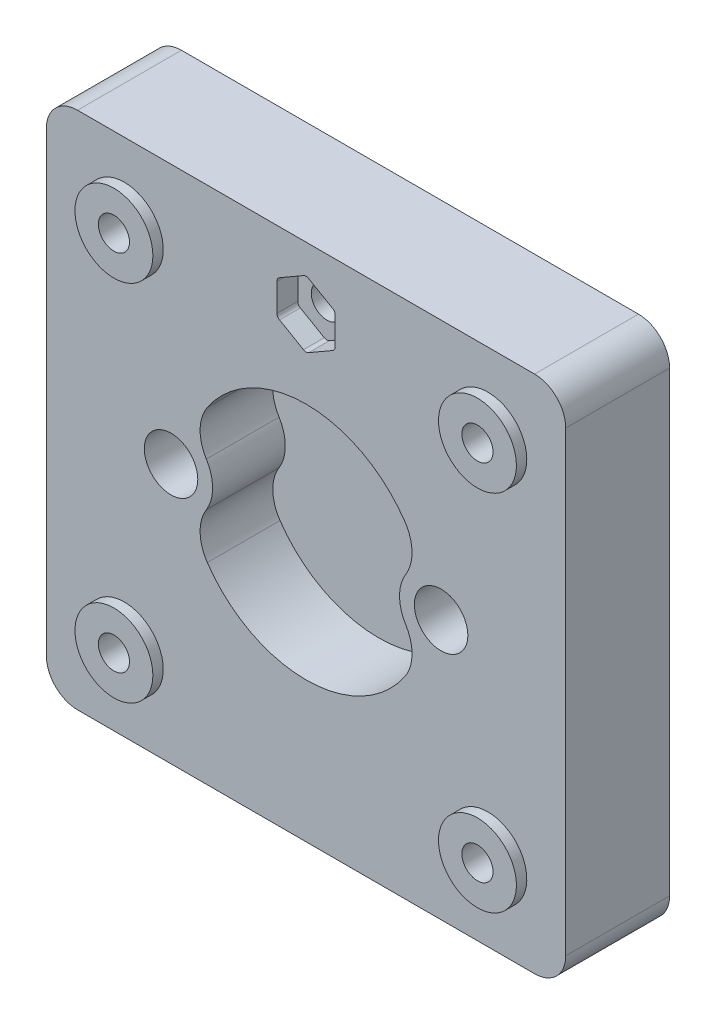
SolidWorks part; units mm, degrees
other "Anode"
ref_plane "Front Plane" through (0, 0, 0) normal (0, 0, 1) x (1, 0, 0)
ref_plane "Top Plane" through (0, 0, 0) normal (0, 1, 0) x (1, 0, 0)
ref_plane "Right Plane" through (0, 0, 0) normal (1, 0, 0) x (0, 0, -1)
sketch "Sketch1" plane through (0, 0, 0) normal (0, 1, 0) x (1, 0, 0)
  line L1 (25, -25) -> (-25, -25)
  line L2 (25, -25) -> (25, 25)
  line L3 (25, 25) -> (-25, 25)
  line L4 (-25, -25) -> (-25, 25)
  line L5 (25, -25) -> (-25, 25) construction
  line L6 (25, 25) -> (-25, -25) construction
  point P0 (0, 0)
  dimension "D1" = 50
  dimension "D2" = 50
extrude "Body" add sketch "Sketch1" along normal blind 10
sketch "Sketch2" plane through (0, 10, 0) normal (0, 1, 0) x (1, 0, 0)
  circle A0 centre (0, 0) radius 11.5
  dimension "D1" = 23
extrude "Cut view" cut sketch "Sketch2" against normal blind 7
fillet "FilletBody" radius 3 4 edges at (-25, 5, -25) (25, 5, -25) (25, 5, 25) (-25, 5, 25)
sketch "Sketch3" plane through (0, 10, 0) normal (0, 1, 0) x (1, 0, 0)
  line L0 (-25, 22) -> (-25, -22) construction
  line L1 (22, 25) -> (-22, 25) construction
  line L2 (-38.934, 0) -> (38.0552, 0) construction
  line L3 (0, 29.5616) -> (0, -31.3312) construction
  circle A0 centre (-17.5, 17.5) radius 3.75
  circle A1 centre (17.5, 17.5) radius 3.75
  circle A2 centre (17.5, -17.5) radius 3.75
  circle A3 centre (-17.5, -17.5) radius 3.75
  dimension "D1" = 7.5
  dimension "D2" = 7.5
  dimension "D3" = 7.5
extrude "Bolt extrude" add sketch "Sketch3" along normal blind 1
sketch "Sketch4" plane through (0, 11, 0) normal (0, 1, 0) x (1, 0, 0)
  line L2 (-40.7589, 0) -> (37.9331, 0) construction
  line L3 (-5.5, 0) -> (5.5, 0) construction
  line L4 (0, 29.2624) -> (0, -30.4072) construction
  circle A0 centre (-17.5, 17.5) radius 1.5
  circle A1 centre (17.5, 17.5) radius 1.5
  circle A2 centre (17.5, -17.5) radius 1.5
  circle A3 centre (-17.5, -17.5) radius 1.5
  dimension "D1" = 3
extrude "Bolt" cut sketch "Sketch4" against normal blind 16 and the other way blind 10
sketch "Sketch5" plane through (0, 10, 0) normal (0, 1, 0) x (1, 0, 0)
  line L0 (22, 25) -> (-22, 25) construction
  line L1 (0, 22.2332) -> (-2.8, 20.6166)
  line L2 (-2.8, 20.6166) -> (-2.8, 17.3834)
  line L3 (-2.8, 17.3834) -> (0, 15.7668)
  line L4 (0, 15.7668) -> (2.8, 17.3834)
  line L5 (2.8, 17.3834) -> (2.8, 20.6166)
  line L6 (2.8, 20.6166) -> (0, 22.2332)
  circle A0 centre (0, 19) radius 2.8 construction
  dimension "D2" = 5.6
  dimension "D1" = 6
extrude "Hex" cut sketch "Sketch5" against normal blind 2
sketch "Sketch19" plane through (0, 8, 0) normal (0, 1, 0) x (1, 0, 0)
  circle A0 centre (0, 19) radius 1.5
  dimension "D1" = 3
extrude "Hex_bolt" cut sketch "Sketch19" against normal blind 3
sketch "Sketch6" plane through (0, 10, 0) normal (0, 1, 0) x (1, 0, 0)
  line L0 (-5.5, 0) -> (5.5, 0) construction
  line L1 (-25, 22) -> (-25, -22) construction
  line L2 (0, 27.3129) -> (0, -30.0369) construction
  circle A0 centre (-13, 0) radius 4
  circle A1 centre (13, 0) radius 4
  dimension "D2" = 8
  dimension "D1" = 12
extrude "Field1" add sketch "Sketch6" against normal blind 7
fillet "Field2" radius 4 4 edges at (10.9712, 6.5, -3.4473) (10.9712, 6.5, 3.4473) (-10.9712, 6.5, 3.4473) (-10.9712, 6.5, -3.4473)
sketch "Sketch7" plane through (0, 10, 0) normal (0, 1, 0) x (1, 0, 0)
  line L0 (-5.5, 0) -> (5.5, 0) construction
  line L1 (-25, 22) -> (-25, -22) construction
  line L2 (0, 27.9755) -> (0, -30.6258) construction
  circle A0 centre (-13, 0) radius 2.575
  circle A1 centre (13, 0) radius 2.575
  dimension "D2" = 5.15
  dimension "D1" = 12
extrude "Ports1" add sketch "Sketch7" along normal blind 12
sketch "Sketch10" plane through (0, 22, 0) normal (0, 1, 0) x (1, 0, 0)
  line L0 (0, 29.9579) -> (0, -31.6237) construction
  circle A0 centre (-13, 0) radius 1.575
  circle A1 centre (13, 0) radius 1.575
  dimension "D1" = 3.15
extrude "Ports2" cut sketch "Sketch10" against normal blind 32 and the other way blind 12
sketch "Sketch11" plane through (0, 0, 0) normal (0, -1, 0) x (1, 0, 0)
  circle A0 centre (0, 0) radius 15
  circle A1 centre (0, 0) radius 20
  dimension "D1" = 30
  dimension "D2" = 40
extrude "Seal1" cut sketch "Sketch11" against normal blind 0.5 contours A1 A0
sketch "Sketch15" plane through (0, 0, 0) normal (0, -1, 0) x (1, 0, 0)
  line L0 (5.5, 0) -> (-5.5, 0) construction
  line L1 (-14, 0) -> (-12, 0)
  line L2 (-8, 0) -> (-6, 0)
  line L3 (3, 0) -> (5, 0)
  line L4 (9, 0) -> (11, 0)
  line L5 (-31.4935, 0) -> (32.7979, 0) construction
  arc A0 (-14, 0) -> (13.523, 3.6235) centre (0, 0) cw
  arc A1 (-8, 0) -> (7.2505, 3.3809) centre (0, 0) cw
  arc A2 (-12, 0) -> (11.5911, 3.1058) centre (0, 0) cw
  arc A3 (-6, 0) -> (5.4378, 2.5357) centre (0, 0) cw
  arc A4 (13.523, 3.6235) -> (11.5911, 3.1058) centre (12.557, 3.3646) cw
  arc A5 (7.2505, 3.3809) -> (5.4378, 2.5357) centre (6.3442, 2.9583) cw
  arc A6 (11, 0) -> (-10.3366, 3.7622) centre (0, 0) ccw
  arc A7 (9, 0) -> (-8.4572, 3.0782) centre (0, 0) ccw
  arc A8 (5, 0) -> (-3.5355, 3.5355) centre (0, 0) ccw
  arc A9 (3, 0) -> (-2.1213, 2.1213) centre (0, 0) ccw
  arc A10 (-10.3366, 3.7622) -> (-8.4572, 3.0782) centre (-9.3969, 3.4202) ccw
  arc A11 (-3.5355, 3.5355) -> (-2.1213, 2.1213) centre (-2.8284, 2.8284) ccw
  arc A12 (3, 0) -> (-2.1213, -2.1213) centre (0, 0) cw
  arc A13 (-3.5355, -3.5355) -> (-2.1213, -2.1213) centre (-2.8284, -2.8284) cw
  arc A14 (5, 0) -> (-3.5355, -3.5355) centre (0, 0) cw
  arc A15 (-8, 0) -> (7.2505, -3.3809) centre (0, 0) ccw
  arc A16 (-6, 0) -> (5.4378, -2.5357) centre (0, 0) ccw
  arc A17 (7.2505, -3.3809) -> (5.4378, -2.5357) centre (6.3442, -2.9583) ccw
  arc A18 (9, 0) -> (-8.4572, -3.0782) centre (0, 0) cw
  arc A19 (-10.3366, -3.7622) -> (-8.4572, -3.0782) centre (-9.3969, -3.4202) cw
  arc A20 (11, 0) -> (-10.3366, -3.7622) centre (0, 0) cw
  arc A21 (-14, 0) -> (13.523, -3.6235) centre (0, 0) ccw
  arc A22 (-12, 0) -> (11.5911, -3.1058) centre (0, 0) ccw
  arc A23 (13.523, -3.6235) -> (11.5911, -3.1058) centre (12.557, -3.3646) ccw
  circle M18 centre (-13, 0) radius 1.575
  dimension "D1" = 165
  dimension "D2" = 155
  dimension "D5" = 14
  dimension "D6" = 8
  dimension "D7" = 160
  dimension "D8" = 11
  dimension "D10" = 5
  dimension "D11" = 135
  dimension "D3" = 2
  dimension "D4" = 2
  dimension "D9" = 2
  dimension "D12" = 2
extrude "FlowField" cut sketch "Sketch15" against normal blind 1.5 contours A4 A0 A2 M18 | A6 A10 A7 L4 | A5 A1 L2 A3 | A8 A11 A9 L3 | A14 L3 A12 A13 | A15 A17 A16 L2 | A20 L4 A18 A19 | A21 A23 A22 M18
sketch "Sketch16" plane through (0, 0, 0) normal (0, -1, 0) x (1, 0, 0)
  line L0 (-13, 0) -> (0, 0) construction
  line L1 (-13, 1) -> (0, 1)
  line L2 (-13, -1) -> (0, -1)
  line L3 (13, 0) -> (4.4291, 0) construction
  line L4 (5.5, 0) -> (-5.5, 0) construction
  line L5 (13, -1) -> (4.4291, -1)
  line L6 (13, 1) -> (4.4291, 1)
  arc A0 (-13, 1) -> (-13, -1) centre (-13, 0) ccw
  arc A1 (0, -1) -> (0, 1) centre (0, 0) ccw
  arc A2 (13, -1) -> (13, 1) centre (13, 0) ccw
  arc A3 (4.4291, 1) -> (4.4291, -1) centre (4.4291, 0) ccw
  point P4 (-6.5, 0)
  point P14 (8.7146, 0)
  dimension "D1" = 1
  dimension "D2" = 1
extrude "FlowField_Channel" cut sketch "Sketch16" against normal blind 1.5
mirror "Mirror3" about plane through (0, 0, 0) normal (0, 1, 0) of bodies 112
delete or keep bodies "Body-Delete/Keep 2" type delete bodies bodies 112
move or copy body "Body-Move/Copy1" bodies to move or copy 117 copy no rotation origin (0, -11, 0) rotation axis (-1, 0, 0) rotation angle 90
move or copy body "Body-Move/Copy2" bodies to move or copy 118 copy no rotation origin (0, -11, 0) rotation axis (0, 0, 1) rotation angle 180
sketch "Sketch20" plane through (0, 0, 11) normal (0, 0, 1) x (1, 0, 0)
  circle A0 centre (-13, -11) radius 2.575 construction
  circle A1 centre (-13, -11) radius 2.575
  circle A2 centre (13, -11) radius 2.575 construction
  circle A3 centre (13, -11) radius 2.575
extrude "Cut-Extrude1" cut sketch "Sketch20" against normal blind 17
fillet "Fillet1" radius 0.5 6 edges at (0, 4.7668, -2) (-2.8, 6.3834, -2) (2.8, 6.3834, -2) (2.8, 9.6166, -2) (-2.8, 9.6166, -2) (0, 11.2332, -2)
